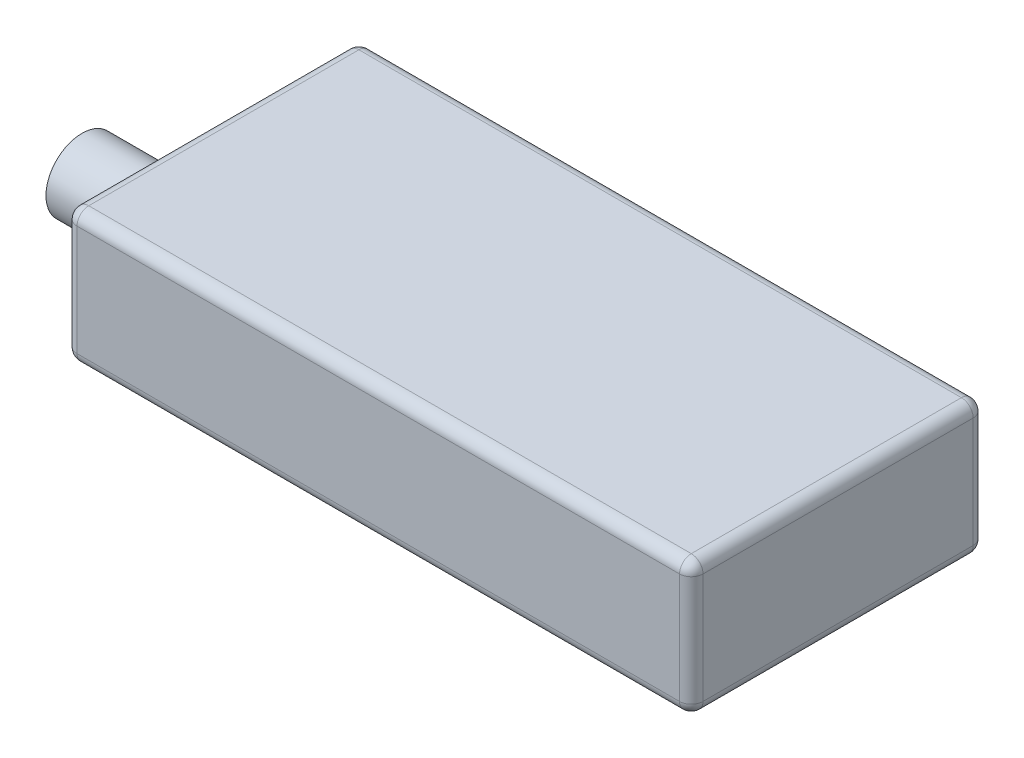
SolidWorks part; units mm, degrees
ref_plane "Front Plane" through (0, 0, 0) normal (0, 0, 1) x (1, 0, 0)
ref_plane "Top Plane" through (0, 0, 0) normal (0, 1, 0) x (1, 0, 0)
ref_plane "Right Plane" through (0, 0, 0) normal (1, 0, 0) x (0, 0, -1)
sketch "Sketch1" plane through (0, 0, 0) normal (0, 1, 0) x (1, 0, 0)
  line L1 (-26.65, -12.5) -> (26.65, -12.5)
  line L2 (-26.65, -12.5) -> (-26.65, 12.5)
  line L3 (-26.65, 12.5) -> (26.65, 12.5)
  line L4 (26.65, -12.5) -> (26.65, 12.5)
  line L5 (-26.65, -12.5) -> (26.65, 12.5) construction
  line L6 (-26.65, 12.5) -> (26.65, -12.5) construction
  point P0 (0, 0)
  dimension "D1" = 53.3
  dimension "D2" = 25
extrude "Boss-Extrude1" add sketch "Sketch1" along normal blind 11.4
fillet "Fillet1" radius 1 12 edges at (26.65, 5.7, -12.5) (-26.65, 5.7, -12.5) (-26.65, 5.7, 12.5) (26.65, 5.7, 12.5) (0, 0, -12.5) (-26.65, 0, 0) (0, 0, 12.5) (26.65, 0, 0) (0, 11.4, 12.5) (-26.65, 11.4, 0) (0, 11.4, -12.5) (26.65, 11.4, 0)
sketch "Sketch2" plane through (-26.65, 0, 0) normal (-1, 0, 0) x (0, 0, 1)
  line L0 (11.5, 0) -> (-11.5, 0) construction
  line L1 (11.5, 1) -> (11.5, 10.4) construction
  circle A0 centre (4.975, 6.865) radius 3.065
  dimension "D1" = 6.13
  dimension "D2" = 6.865
  dimension "D3" = 6.525
extrude "Boss-Extrude2" add sketch "Sketch2" along normal blind 6.1
equation "\"D2@Sketch2\"=3.8+\"D1@Sketch2\"/2"
equation "\"D3@Sketch2\"=3.46+\"D1@Sketch2\"/2"
